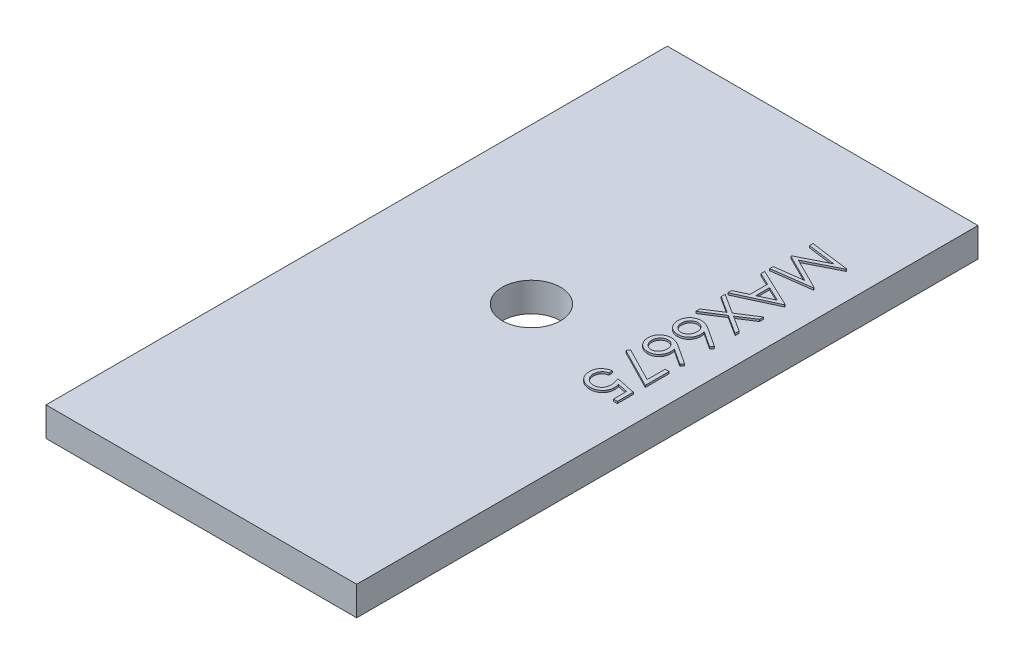
SolidWorks part; units mm, degrees
ref_plane "Front Plane" through (0, 0, 0) normal (0, 0, 1) x (1, 0, 0)
ref_plane "Top Plane" through (0, 0, 0) normal (0, 1, 0) x (1, 0, 0)
ref_plane "Right Plane" through (0, 0, 0) normal (1, 0, 0) x (0, 0, -1)
sketch "Sketch1" plane through (0, 0, 0) normal (0, 1, 0) x (1, 0, 0)
  line L1 (8, -16) -> (-8, -16)
  line L2 (8, -16) -> (8, 16)
  line L3 (8, 16) -> (-8, 16)
  line L4 (-8, -16) -> (-8, 16)
  line L5 (8, -16) -> (-8, 16) construction
  line L6 (8, 16) -> (-8, -16) construction
  point P0 (0, 0)
  dimension "D1" = 16
  dimension "D2" = 32
extrude "Boss-Extrude1" add sketch "Sketch1" along normal blind 1.5
sketch "Sketch2" plane through (0, 1.5, 0) normal (0, 1, 0) x (1, 0, 0)
  line L0 (8, 16) -> (-8, 16) construction
  line L1 (8, -16) -> (8, 16) construction
  circle A0 centre (0, 1) radius 1.5
  dimension "D3" = 3
  dimension "D1" = 15
  dimension "D2" = 8
extrude "Cut-Extrude1" cut sketch "Sketch2" against normal through all
sketch "Sketch4" plane through (0, 1.5, 0) normal (0, 1, 0) x (1, 0, 0)
  line L0 (4.6579, 11) -> (4.6579, -13.2618) construction
  line L1 (8, 16) -> (-8, 16) construction
  text T0 "MAX6675" font "Century Gothic" height 2
  dimension "D1" = 5
extrude "Boss-Extrude2" add sketch "Sketch4" along normal blind 0.1
